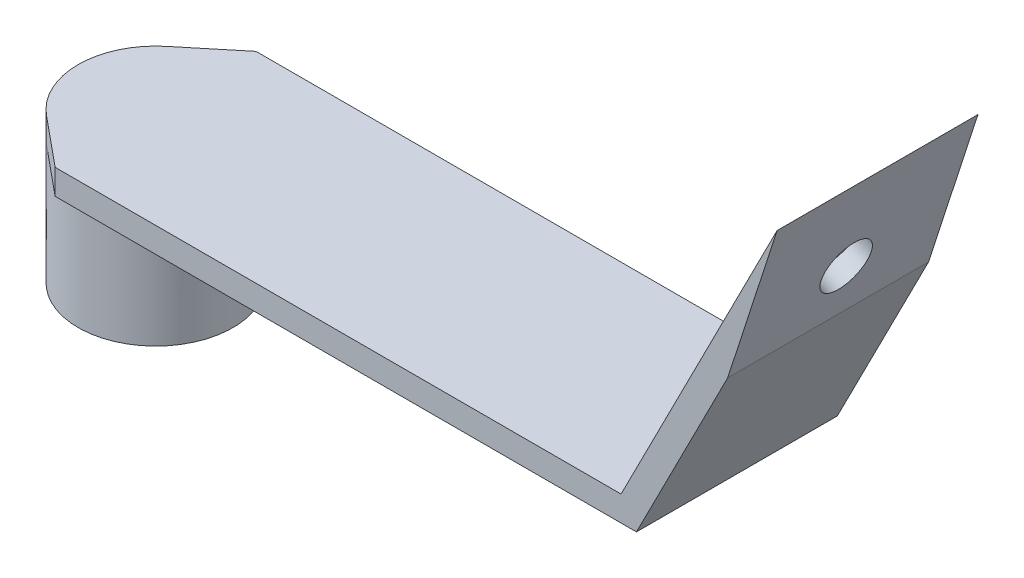
SolidWorks part; units mm, degrees
ref_plane "Front" through (0, 0, 0) normal (0, 0, 1) x (1, 0, 0)
ref_plane "Top" through (0, 0, 0) normal (0, 1, 0) x (1, 0, 0)
ref_plane "Right" through (0, 0, 0) normal (1, 0, 0) x (0, 0, -1)
sketch "Sketch1" plane through (0, 0, 0) normal (0, 0, 1) x (1, 0, 0)
  line L0 (-92.4958, -3.4222) -> (-20.9415, -3.4222)
  line L1 (-20.9415, -3.4222) -> (-1.2089, 35.3052)
  line L3 (-92.4958, -6.5972) -> (-18.9958, -6.5972)
  line L6 (-92.4958, -3.4222) -> (-92.4958, -6.5972)
  line L8 (-7.4645, 16.0344) -> (-1.2089, 35.3052)
  line L9 (-1.2089, 35.3052) -> (23.8053, 30.1317) construction
  line L10 (0.5203, 31.7054) -> (23.1623, 27.0225) construction
  line L11 (-18.9958, -6.5972) -> (-7.4645, 16.0344)
  line L12 (-18.9958, -6.5972) -> (0.5203, 31.7054) construction
  dimension "D2" = 73.5
  dimension "D3" = 25.4
  dimension "D4" = 117
  dimension "D1" = 3.175
extrude "Boss-Extrude1" add sketch "Sketch1" along normal blind 25.4
sketch "Sketch2" plane through (0, -3.4222, 0) normal (0, 1, 0) x (1, 0, 0)
  line L0 (-92.4958, -25.4) -> (-92.4958, 0) construction
  circle A0 centre (-92.4958, -12.7) radius 7.0714
  circle A1 centre (-92.4958, -12.7) radius 9.8014
extrude "Boss-Extrude2" add sketch "Sketch2" against normal blind 19
sketch "Sketch3" plane through (0, -3.4222, 0) normal (0, 1, 0) x (1, 0, 0)
  line L0 (-92.4958, 0) -> (-98.7286, -5.1356)
  line L1 (-98.7286, -5.1356) -> (-98.7286, -20.2644)
  line L2 (-98.7286, -20.2644) -> (-92.4958, -25.4)
  line L3 (-92.4958, 0) -> (-92.4958, -25.4)
  line L4 (-98.7286, -5.1356) -> (-102.2973, -12.7)
  line L5 (-102.2973, -12.7) -> (-98.7286, -20.2644)
  arc A0 (-92.4958, -2.8986) -> (-92.4958, -22.5014) centre (-92.4958, -12.7) ccw construction
  line M1 (-92.4958, 0) -> (-92.4958, -2.8986)
  arc M2 (-92.4958, -2.8986) -> (-92.4958, -22.5014) centre (-92.4958, -12.7) ccw
  line M3 (-92.4958, -22.5014) -> (-92.4958, -25.4)
  arc M7 (-92.4958, -19.7714) -> (-92.4958, -5.6286) centre (-92.4958, -12.7) cw
  line M8 (-92.4958, -5.6286) -> (-92.4958, -19.7714)
extrude "Boss-Extrude3" add sketch "Sketch3" against normal blind 3.175 contours L1 M7 | L4 L5 L1 M7 | L3 L1 M7 M2 | L2 M2 M3 | L1 M7 M8 | L3 L1 M2 M7 | L0 M1 M2
sketch "Sketch4" plane through (-15.241, 7.7657, 0) normal (-0.891, 0.454, 0) x (0, 0, 1)
  line L0 (25.4, 30.9084) -> (25.4, -12.5564) construction
  line L1 (25.4, 30.9084) -> (0, 30.9084) construction
  circle A0 centre (12.7, 18.2084) radius 3.175
  dimension "D1" = 6.35
  dimension "D2" = 12.7
  dimension "D3" = 12.7
extrude "Cut-Extrude1" cut sketch "Sketch4" against normal blind 3.175
